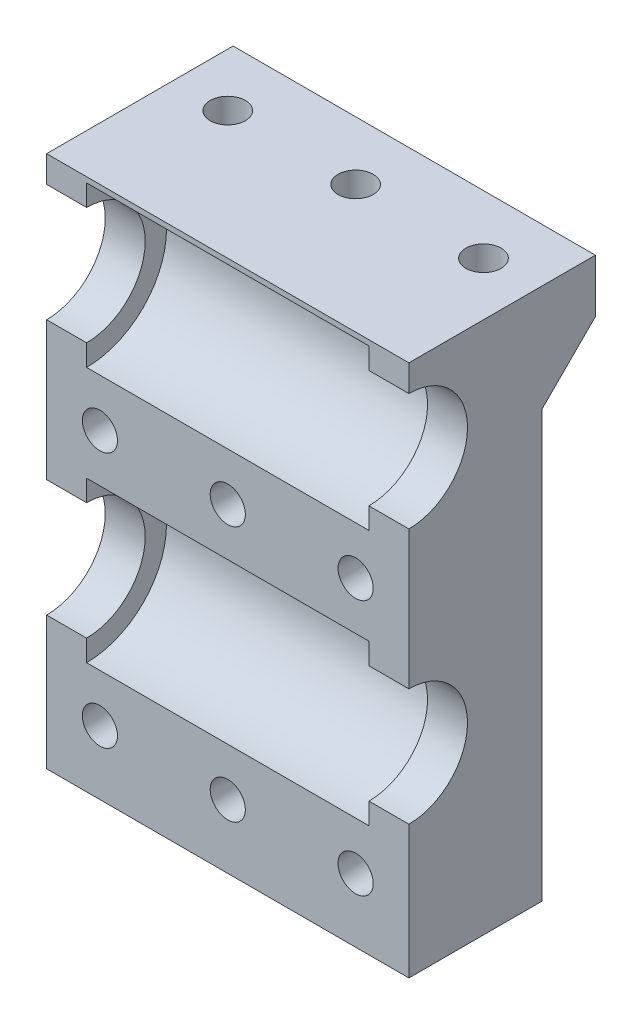
SolidWorks part; units mm, degrees
ref_plane "前视基准面" through (0, 0, 0) normal (0, 0, 1) x (1, 0, 0)
ref_plane "上视基准面" through (0, 0, 0) normal (0, 1, 0) x (1, 0, 0)
ref_plane "右视基准面" through (0, 0, 0) normal (1, 0, 0) x (0, 0, -1)
sketch "草图1" plane through (0, 0, 0) normal (1, 0, 0) x (0, 0, -1)
  line L1 (0, 0) -> (12.5, 0)
  line L2 (0, 0) -> (0, 50)
  line L3 (0, 50) -> (12.5, 50)
  line L4 (12.5, 0) -> (12.5, 50)
  dimension "D1" = 50
  dimension "D2" = 12.5
extrude "凸台-拉伸1" add sketch "草图1" along normal blind 34
ref_plane "基准面1" through (17, 0, 0) normal (-1, 0, 0) x (0, 0, 1)
sketch "草图2" plane through (17, 0, 0) normal (-1, 0, 0) x (0, 0, 1)
  line L0 (0, 50) -> (0, 0) construction
  line L1 (0, 0) -> (-12.5, 0) construction
  circle A0 centre (0, 18) radius 7.5
  circle A1 centre (0, 42) radius 7.5
  dimension "D1" = 15
  dimension "D2" = 15
  dimension "D3" = 18
  dimension "D4" = 24
extrude "切除-拉伸1" cut sketch "草图2" against normal mid plane 26.5
sketch "草图3" plane through (0, 0, -12.5) normal (0, 0, -1) x (-1, 0, 0)
  line L0 (-34, 0) -> (-34, 50) construction
  line L1 (0, 0) -> (0, 50) construction
  line L2 (-34, 0) -> (0, 0) construction
  line L3 (-17, -9.625) -> (-17, 9.625) construction
  circle A0 centre (-29, 30) radius 1.65
  circle A1 centre (-5, 30) radius 1.65
  circle A4 centre (-17, 30) radius 1.65
  dimension "D1" = 3.3
  dimension "D2" = 3.3
  dimension "D8" = 3.3
  dimension "D3" = 5
  dimension "D4" = 5
  dimension "D5" = 30
  dimension "D6" = 30
  dimension "D9" = 30
extrude "切除-拉伸2" cut sketch "草图3" against normal through all both and the other way through all
sketch "草图4" plane through (0, 0, -12.5) normal (0, 0, -1) x (-1, 0, 0)
  circle A1 centre (-29, 30) radius 2.9
  circle A2 centre (-5, 30) radius 2.9
  dimension "D1" = 5.8
  dimension "D2" = 5.8
extrude "切除-拉伸3" cut sketch "草图4" against normal blind 4.5
sketch "草图5" plane through (34, 0, 0) normal (1, 0, 0) x (0, 0, -1)
  line L0 (0, 50) -> (0, 0) construction
  line L1 (0, 0) -> (12.5, 0) construction
  circle A0 centre (0, 18) radius 5.5
  circle A1 centre (0, 42) radius 5.5
  dimension "D1" = 11
  dimension "D2" = 11
  dimension "D3" = 18
  dimension "D4" = 24
extrude "切除-拉伸4" cut sketch "草图5" against normal through all
sketch "草图6" plane through (17, 0, 0) normal (-1, 0, 0) x (0, 0, 1)
  line L0 (-12.5, 50) -> (-17.5, 50)
  line L1 (-17.5, 50) -> (-17.5, 45)
  line L2 (-17.5, 45) -> (-12.5, 40)
  line L3 (-12.5, 0) -> (-12.5, 50) construction
  line L4 (-12.5, 40) -> (-12.5, 50)
  dimension "D1" = 10
  dimension "D2" = 5
  dimension "D3" = 45
extrude "凸台-拉伸2" add sketch "草图6" along normal mid plane 34
ref_plane "基准面2" through (0, 45, 0) normal (0, 1, 0) x (1, 0, 0)
sketch "草图9" plane through (0, 45, 0) normal (0, 1, 0) x (1, 0, 0)
  line L0 (5, 8) -> (5, 12.5) construction
  line L1 (17, 9.625) -> (17, -9.625) construction
  line L2 (29, 0) -> (29, 8) construction
  line L4 (30.25, 0) -> (3.75, 0) construction
  circle A0 centre (5, 12) radius 1.65
  circle A1 centre (17, 12) radius 1.65
  circle A2 centre (29, 12) radius 1.65
  dimension "D1" = 3.3
  dimension "D2" = 3.3
  dimension "D3" = 3.3
  dimension "D4" = 12
  dimension "D5" = 12
  dimension "D6" = 12
extrude "切除-拉伸6" cut sketch "草图9" along normal through all
sketch "草图7" plane through (0, 45, 0) normal (0, 1, 0) x (1, 0, 0)
  line L0 (5, 8) -> (5, 12.5) construction
  line L1 (7.85, 10.3546) -> (7.85, 13.0908)
  line L4 (2.15, 12.982) -> (2.15, 10.3546)
  line L5 (2.15, 10.3546) -> (5, 8.7091)
  line L6 (5, 8.7091) -> (7.85, 10.3546)
  line L7 (17, 9.625) -> (17, -9.625) construction
  line L8 (19.85, 10.3546) -> (19.85, 13.091)
  line L11 (14.15, 12.982) -> (14.15, 10.3546)
  line L12 (14.15, 10.3546) -> (17, 8.7091)
  line L13 (17, 8.7091) -> (19.85, 10.3546)
  line L14 (29, 8) -> (29, 12.5) construction
  line L15 (31.85, 10.3546) -> (31.85, 13.091)
  line L18 (26.15, 12.982) -> (26.15, 10.3546)
  line L19 (26.15, 10.3546) -> (29, 8.7091)
  line L20 (29, 8.7091) -> (31.85, 10.3546)
  line L21 (0, 17.5) -> (34, 17.5) construction
  line L22 (0, 17.5) -> (0, 0) construction
  line L23 (2.15, 12.982) -> (2.15, 17.5)
  line L24 (2.15, 17.5) -> (7.85, 17.5)
  line L25 (7.85, 17.5) -> (7.85, 13.0908)
  line L26 (14.15, 12.982) -> (14.15, 17.5)
  line L27 (14.15, 17.5) -> (19.85, 17.5)
  line L28 (19.85, 17.5) -> (19.85, 13.091)
  line L29 (26.15, 12.982) -> (26.15, 17.5)
  line L30 (26.15, 17.5) -> (31.85, 17.5)
  line L31 (31.85, 17.5) -> (31.85, 13.091)
  line L32 (4.8972, 15.2315) -> (3.4972, 14.4232) [skipped]
  line L33 (7.7472, 13.7048) -> (6.3472, 14.5131) [skipped]
  line L34 (16.8972, 15.2315) -> (15.4972, 14.4232) [skipped]
  line L35 (19.7472, 13.7048) -> (18.3472, 14.5131) [skipped]
  line L36 (28.8972, 15.2315) -> (27.4972, 14.4232) [skipped]
  line L37 (31.7472, 13.7048) -> (30.3472, 14.5131) [skipped]
  circle A0 centre (5, 12) radius 2.85 construction
  circle A1 centre (17, 12) radius 2.85 construction
  circle A2 centre (29, 12) radius 2.85 construction
  circle A3 centre (5, 12) radius 1.65 construction
  circle A4 centre (17, 12) radius 1.65 construction
  circle A5 centre (29, 12) radius 1.65 construction
  dimension "D1" = 5.7
  dimension "D2" = 5.7
  dimension "D3" = 5.7
extrude "切除-拉伸5" cut sketch "草图7" against normal blind 9
pattern_linear "阵列(线性)1" count 2 spacing 24 along (0, -1, 0) of "切除-拉伸2"
